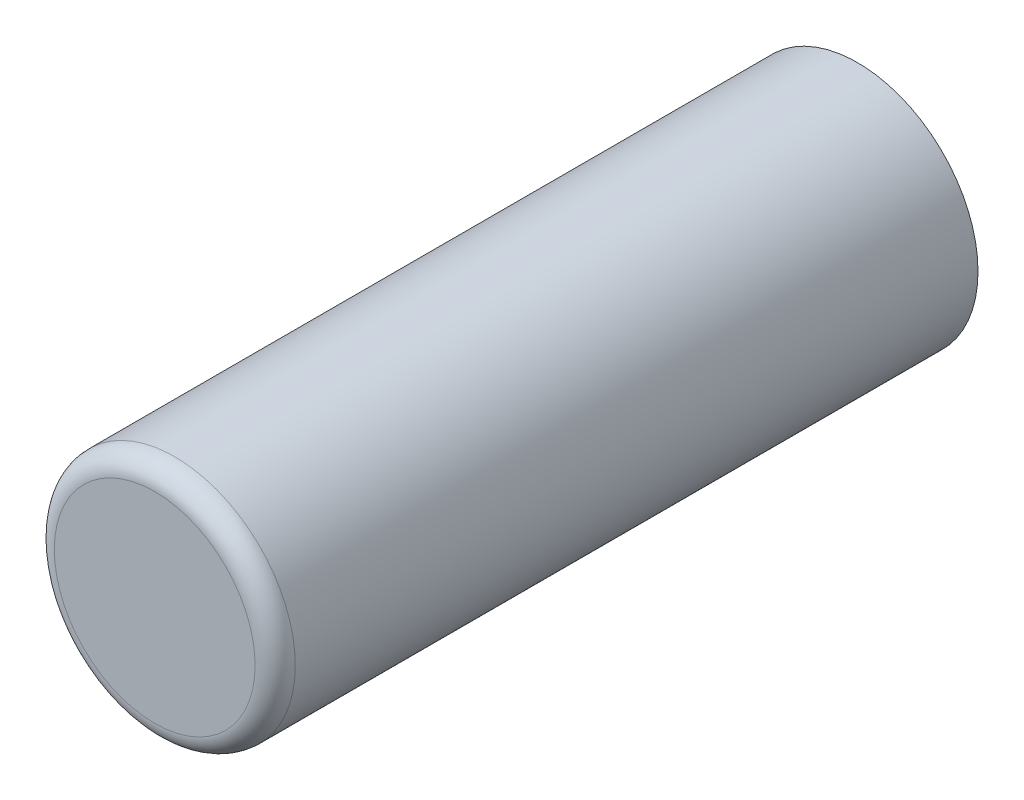
SolidWorks part; units mm, degrees
ref_plane "Front Plane" through (0, 0, 0) normal (0, 0, 1) x (1, 0, 0)
ref_plane "Top Plane" through (0, 0, 0) normal (0, 1, 0) x (1, 0, 0)
ref_plane "Right Plane" through (0, 0, 0) normal (1, 0, 0) x (0, 0, -1)
sketch "Sketch1" plane through (0, 0, 0) normal (0, 0, 1) x (1, 0, 0)
  circle A0 centre (0, 0) radius 4.8
  dimension "D1" = 9.6
extrude "Boss-Extrude1" add sketch "Sketch1" along normal mid plane 28
fillet "Fillet1" radius 0.8 1 edges at (4.8, 0, 14)
